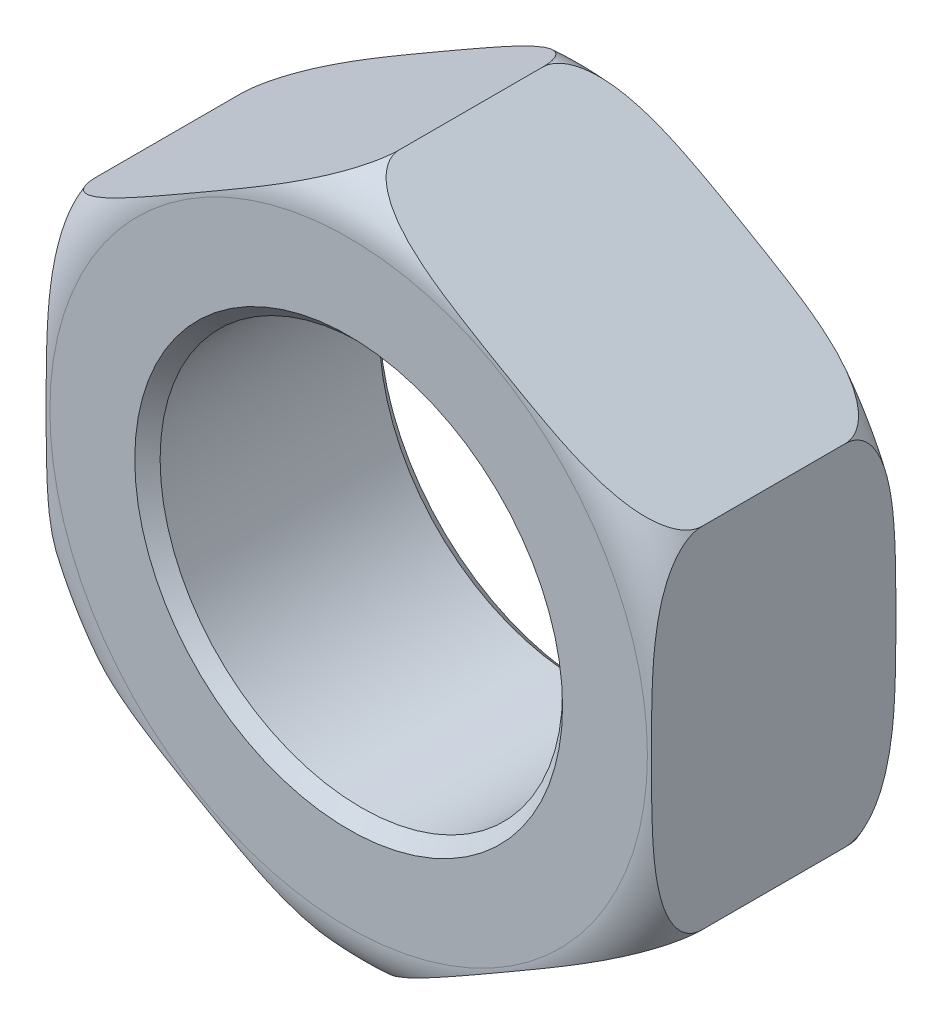
SolidWorks part; units mm, degrees
ref_plane "Front" through (0, 0, 0) normal (0, 0, 1) x (1, 0, 0)
ref_plane "Top" through (0, 0, 0) normal (0, 1, 0) x (1, 0, 0)
ref_plane "Right" through (0, 0, 0) normal (1, 0, 0) x (0, 0, -1)
sketch "Sketch1" plane through (0, 0, 0) normal (0, 0, 1) x (1, 0, 0)
  line L1 (0, 13.7848) -> (-11.938, 6.8924)
  line L2 (-11.938, 6.8924) -> (-11.938, -6.8924)
  line L3 (-11.938, -6.8924) -> (0, -13.7848)
  line L4 (0, -13.7848) -> (11.938, -6.8924)
  line L5 (11.938, -6.8924) -> (11.938, 6.8924)
  line L6 (11.938, 6.8924) -> (0, 13.7848)
  circle A0 centre (0, 0) radius 11.938 construction
  circle A1 centre (0, 0) radius 7.9375
  dimension "NN" = 15.875
  dimension "A" = 23.876
extrude "Extrude1" add sketch "Sketch1" along normal mid plane 9.652
sketch "Sketch2" plane through (0, 0, 0) normal (1, 0, 0) x (0, 0, -1)
  line L0 (0, 0) -> (6.5147, 0) construction
  line L1 (0, 0) -> (0, 14.8511) construction
  line L2 (4.826, 7.9375) -> (4.826, 8.4375)
  line L4 (4.826, 8.4375) -> (4.326, 7.9375)
  line L6 (4.326, 7.9375) -> (4.826, 7.9375)
  line L7 (4.826, 13.7848) -> (4.826, 11.7848)
  line L10 (2.826, 13.7848) -> (4.826, 13.7848)
  line L11 (-2.826, 13.7848) -> (-4.826, 13.7848)
  line L12 (-4.826, 13.7848) -> (-4.826, 11.7848)
  line L13 (-4.326, 7.9375) -> (-4.826, 7.9375)
  line L14 (-4.826, 8.4375) -> (-4.326, 7.9375)
  line L15 (-4.826, 7.9375) -> (-4.826, 8.4375)
  line L16 (-4.826, 6.8924) -> (-4.826, 13.7848) construction
  line L17 (-4.826, 13.7848) -> (4.826, 13.7848) construction
  line L31 (-4.826, -6.8924) -> (-4.826, 6.8924) construction
  line L32 (4.826, 7.9375) -> (-4.826, 7.9375) construction
  arc A0 (4.826, 11.7848) -> (2.826, 13.7848) centre (2.826, 11.7848) ccw
  arc A1 (-4.826, 11.7848) -> (-2.826, 13.7848) centre (-2.826, 11.7848) cw
  dimension "D1" = 2
  dimension "D2" = 0.5
revolve "Detail" cut sketch "Sketch2" angle 360 about L0
